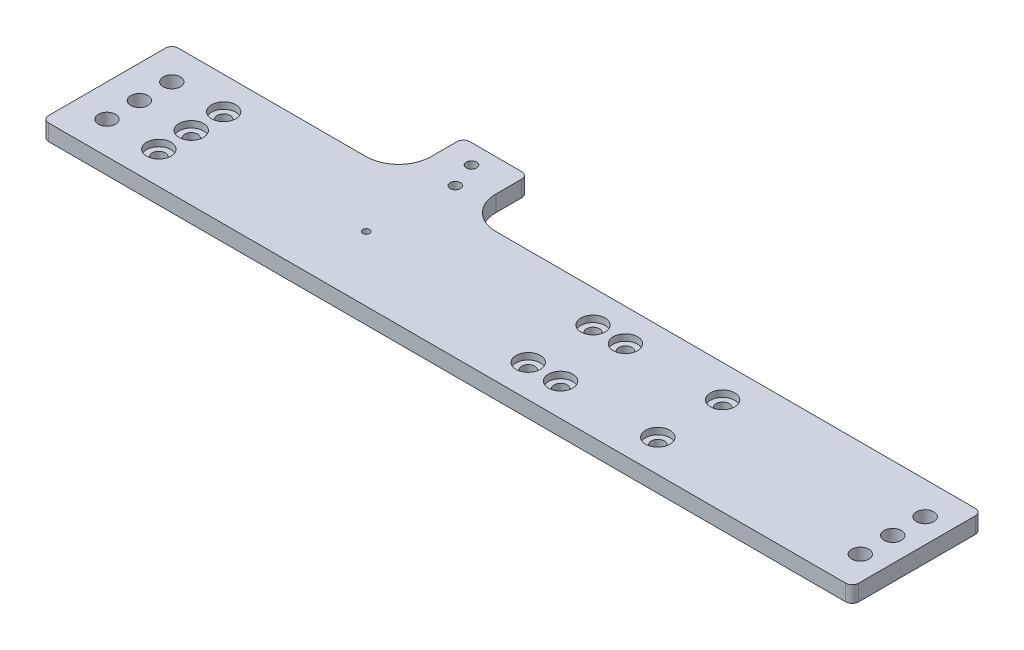
SolidWorks part; units mm, degrees
material "6061-T6 (SS)"
ref_plane "Front" through (0, 0, 0) normal (0, 0, 1) x (1, 0, 0)
ref_plane "Top" through (0, 0, 0) normal (0, 1, 0) x (1, 0, 0)
ref_plane "Right" through (0, 0, 0) normal (1, 0, 0) x (0, 0, -1)
sketch "Sketch1" plane through (0, 0, 0) normal (0, 1, 0) x (1, 0, 0)
  line L1 (-158.75, -25.4) -> (158.75, -25.4)
  line L2 (-158.75, -25.4) -> (-158.75, 25.4)
  line L3 (-158.75, 25.4) -> (158.75, 25.4)
  line L4 (158.75, -25.4) -> (158.75, 25.4)
  line L5 (-158.75, -25.4) -> (158.75, 25.4) construction
  line L6 (-158.75, 25.4) -> (158.75, -25.4) construction
  point P0 (0, 0)
  dimension "D1" = 50.8
  dimension "D2" = 317.5
extrude "Boss-Extrude1" add sketch "Sketch1" along normal blind 6.35
hole_wizard "CBORE for #10 Socket Head Cap Screw1" positions "Sketch2" profile "Sketch4" counterbore size "#10" standard "ANSI Inch" end condition through all
sketch "Sketch2" plane through (0, 6.35, 0) normal (0, 1, 0) x (1, 0, 0)
  line L2 (158.75, 25.4) -> (-158.75, 25.4) construction
  line L6 (-158.75, -25.4) -> (158.75, -25.4) construction
  line L8 (-158.75, 25.4) -> (-158.75, -25.4) construction
  line L12 (158.75, -25.4) -> (158.75, 25.4) construction
  line L15 (19.05, 12.7) -> (19.05, 25.4) construction
  line L17 (19.05, -12.7) -> (19.05, -25.4) construction
  line L18 (-125.73, -25.4) -> (-125.73, -12.7) construction
  line L20 (-125.73, 0) -> (-125.73, 12.7) construction
  line L21 (-125.73, 12.7) -> (-125.73, 25.4) construction
  line L22 (-125.73, 0) -> (-125.73, -12.7) construction
  point P64 (19.05, 12.7)
  point P66 (69.85, 12.7)
  point P68 (19.05, -12.7)
  point P70 (69.85, -12.7)
  point P92 (-125.73, 12.7)
  point P94 (-125.73, 0)
  point P102 (-125.73, -12.7)
  point P127 (31.75, 12.7)
  point P129 (31.75, -12.7)
  dimension "D1" = 38.1
  dimension "D2" = 50.8
  dimension "D3" = 25.4
  dimension "D4" = 88.9
  dimension "D5" = 33.02
sketch "Sketch4" plane through (31.75, 6.35, 12.7) normal (1, 0, 0) x (0, 0, 1)
  line L0 (0, 0) -> (0, 6.35)
  line L1 (0, 6.35) -> (2.5527, 6.35)
  line L3 (2.5527, 6.35) -> (2.5527, 2.54)
  line L4 (2.5527, 2.54) -> (4.7625, 2.54)
  line L5 (4.7625, 2.54) -> (4.7625, 0)
  line L7 (4.7625, 0) -> (0, 0)
  line L11 (0, -6.35) -> (0, 107.95) construction
  dimension "Thru Hole Dia." = 5.1054
  dimension "Thru Hole Depth" = 6.35
  dimension "C'Bore Dia." = 9.525
  dimension "C'Bore Depth" = 2.54
sketch "Sketch7" plane through (0, 0, 0) normal (0, -1, 0) x (1, 0, 0)
  line L0 (-146.05, 25.4) -> (-146.05, 12.7) construction
  line L1 (-158.75, 25.4) -> (158.75, 25.4) construction
  line L2 (-146.05, 12.7) -> (-146.05, 0) construction
  line L3 (-146.05, 0) -> (-146.05, -12.7) construction
  line L4 (-146.05, -12.7) -> (-146.05, -25.4) construction
  line L5 (158.75, -25.4) -> (-158.75, -25.4) construction
  line L7 (-158.75, -25.4) -> (-158.75, 25.4) construction
  line L8 (149.225, 25.4) -> (149.225, 12.7) construction
  line L9 (149.225, 12.7) -> (149.225, 0) construction
  line L10 (149.225, 0) -> (149.225, -12.7) construction
  line L11 (149.225, -12.7) -> (149.225, -25.4) construction
  line L13 (158.75, 25.4) -> (158.75, -25.4) construction
  point P0 (-146.05, 12.7)
  point P2 (-146.05, 0)
  point P4 (-146.05, -12.7)
  point P6 (149.225, 12.7)
  point P8 (149.225, 0)
  point P10 (149.225, -12.7)
  dimension "D1" = 12.7
  dimension "D2" = 9.525
hole_wizard "1/4 Clearance Hole2" positions "Sketch7" profile "Sketch6" hole size "1/4" standard "ANSI Inch" end condition through all
sketch "Sketch6" plane through (-146.05, 0, 12.7) normal (1, 0, 0) x (0, 0, -1)
  line L0 (0, 0) -> (0, 6.35)
  line L1 (0, 6.35) -> (3.3782, 6.35)
  line L2 (3.3782, 6.35) -> (3.3782, 0)
  line L5 (3.3782, 0) -> (0, 0)
  line L11 (0, -6.35) -> (0, 107.95) construction
  dimension "Thru Hole Dia." = 6.7564
  dimension "Thru Hole Depth" = 6.35
sketch "Sketch10" plane through (0, 0, 0) normal (0, -1, 0) x (-1, 0, 0)
  line L0 (158.75, 25.4) -> (158.75, -25.4) construction
  point P0 (57.15, 0)
  dimension "D1" = 101.6
hole_wizard "#6-32 Tapped Hole1" positions "Sketch10" profile "Sketch9" tap size "#6-32" standard "ANSI Inch" end condition through all
sketch "Sketch9" plane through (-57.15, 0, 0) normal (1, 0, 0) x (0, 0, -1)
  line L0 (0, 0) -> (0, 6.35)
  line L1 (0, 6.35) -> (1.3525, 6.35)
  line L2 (1.3525, 6.35) -> (1.3525, 0)
  line L5 (1.3525, 0) -> (0, 0)
  line L11 (0, -6.35) -> (0, 107.95) construction
  dimension "Thru Tap Drill Dia." = 2.7051
  dimension "Thru Tap Drill Depth" = 6.35
cosmetic thread "Hole Thread1" parameters "D2"=3.5052
sketch "Sketch11" plane through (0, 0, 0) normal (0, -1, 0) x (1, 0, 0)
  line L0 (158.75, -25.4) -> (-158.75, -25.4) construction
  line L1 (-70.0118, -25.4) -> (-48.1024, -25.4)
  line L2 (-70.0118, -25.4) -> (-70.0118, -45.81)
  line L3 (-70.0118, -45.81) -> (-48.1024, -45.81)
  line L4 (-48.1024, -25.4) -> (-48.1024, -45.81)
extrude "Boss-Extrude2" [suppressed] add sketch "Sketch11" against normal up to surface (6.35 mm away)
sketch "Sketch12" plane through (0, 6.35, 0) normal (0, 1, 0) x (1, 0, 0)
  line L5 (-158.75, 25.4) -> (-158.75, -25.4) construction
  line L6 (-69.85, 25.4) -> (-69.85, 50.8)
  line L7 (158.75, 25.4) -> (-158.75, 25.4) construction
  line L8 (-69.85, 50.8) -> (-44.45, 50.8)
  line L9 (-44.45, 50.8) -> (-44.45, 25.4)
  line L10 (-69.85, 25.4) -> (-44.45, 25.4)
  dimension "D4" = 88.9
  dimension "D5" = 25.4
  dimension "D6" = 25.4
extrude "Boss-Extrude3" add sketch "Sketch12" against normal up to surface (6.35 mm away) up to face at (-57.15, 0, -1.3526)
sketch "Sketch15" plane through (0, 0, 0) normal (0, -1, 0) x (-1, 0, 0)
  point P0 (59.055, 43.18)
  point P3 (55.245, 33.02)
hole_wizard "#10-32 Tapped Hole1" positions "Sketch15" profile "Sketch14" tap size "#10-32" standard "ANSI Inch" end condition through all
sketch "Sketch14" plane through (-59.055, 0, -43.18) normal (1, 0, 0) x (0, 0, -1)
  line L0 (0, 0) -> (0, 6.35)
  line L1 (0, 6.35) -> (2.0193, 6.35)
  line L2 (2.0193, 6.35) -> (2.0193, 0)
  line L5 (2.0193, 0) -> (0, 0)
  line L11 (0, -6.35) -> (0, 107.95) construction
  dimension "Thru Tap Drill Dia." = 4.0386
  dimension "Thru Tap Drill Depth" = 6.35
fillet "Fillet1" radius 12.7 2 edges at (-44.45, 3.175, -25.4) (-69.85, 3.175, -25.4)
fillet "Fillet2" radius 2.54 6 edges at (158.75, 3.175, -25.4) (158.75, 3.175, 25.4) (-158.75, 3.175, 25.4) (-158.75, 3.175, -25.4) (-69.85, 3.175, -50.8) (-44.45, 3.175, -50.8)
